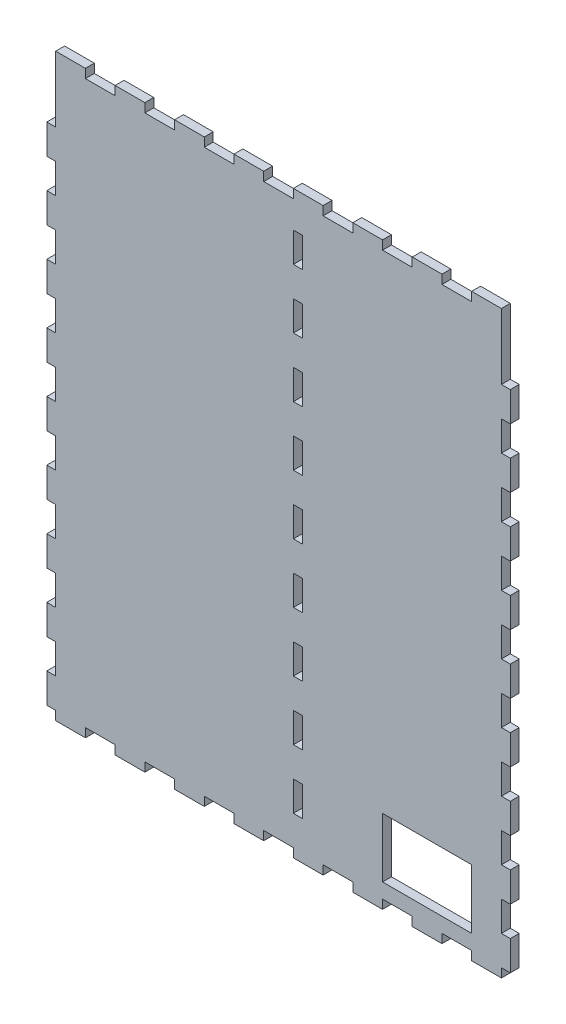
SolidWorks part; units mm, degrees
ref_plane "Plan de face" through (0, 0, 0) normal (0, 0, 1) x (1, 0, 0)
ref_plane "Plan de dessus" through (0, 0, 0) normal (0, 1, 0) x (1, 0, 0)
ref_plane "Plan de droite" through (0, 0, 0) normal (1, 0, 0) x (0, 0, -1)
sketch "Esquisse1" plane through (0, 0, 0) normal (0, 0, 1) x (1, 0, 0)
  line L1 (0, 0) -> (150, 0)
  line L2 (0, 0) -> (0, -189.15)
  line L3 (0, -189.15) -> (150, -189.15)
  line L4 (150, 0) -> (150, -189.15)
  dimension "D1" = 150
  dimension "D2" = 189.15
extrude "Boss.-Extru.1" add sketch "Esquisse1" along normal blind 3
sketch "Esquisse2" plane through (0, 0, 0) normal (0, 1, 0) x (1, 0, 0)
  line L0 (150, -3) -> (0, -3) construction
  line L1 (0, 0) -> (10, 0)
  line L2 (0, 0) -> (0, -3)
  line L3 (0, -3) -> (10, -3)
  line L4 (10, 0) -> (10, -3)
  dimension "D1" = 10
extrude "Boss.-Extru.2" add sketch "Esquisse2" along normal blind 3
pattern_linear "Répétition linéaire1" count 8 spacing 20 along (1, 0, 0) of "Boss.-Extru.2"
sketch "Esquisse3" plane through (0, -189.15, 0) normal (0, -1, 0) x (1, 0, 0)
  line L0 (0, 0) -> (150, 0) construction
  line L1 (0, 3) -> (10, 3)
  line L2 (0, 3) -> (0, 0)
  line L3 (0, 0) -> (10, 0)
  line L4 (10, 3) -> (10, 0)
  dimension "D1" = 10
extrude "Boss.-Extru.3" add sketch "Esquisse3" along normal blind 3
pattern_linear "Répétition linéaire2" count 8 spacing 20 along (1, 0, 0) of "Boss.-Extru.3"
sketch "Esquisse4" plane through (0, 0, 0) normal (-1, 0, 0) x (0, 0, 1)
  line L0 (3, 3) -> (3, -192.15) construction
  line L1 (3, -179.15) -> (0, -179.15)
  line L2 (3, -179.15) -> (3, -189.15)
  line L3 (3, -189.15) -> (0, -189.15)
  line L4 (0, -179.15) -> (0, -189.15)
  line L5 (0, 3) -> (0, -192.15) construction
  line L7 (3, -192.15) -> (0, -192.15) construction
  dimension "D1" = 10
  dimension "D2" = 3
extrude "Boss.-Extru.4" add sketch "Esquisse4" along normal blind 3
pattern_linear "Répétition linéaire3" count 9 spacing 20 along (0, 1, 0) of "Boss.-Extru.4"
sketch "Esquisse5" plane through (150, 0, 0) normal (1, 0, 0) x (0, 0, -1)
  line L0 (-3, -192.15) -> (-3, 3) construction
  line L1 (-3, -189.15) -> (0, -189.15)
  line L2 (-3, -189.15) -> (-3, -179.15)
  line L3 (-3, -179.15) -> (0, -179.15)
  line L4 (0, -189.15) -> (0, -179.15)
  line L5 (0, -192.15) -> (0, 3) construction
  line L8 (0, -192.15) -> (-3, -192.15) construction
  dimension "D1" = 10
  dimension "D2" = 3
extrude "Boss.-Extru.5" add sketch "Esquisse5" along normal blind 3
pattern_linear "Répétition linéaire4" count 9 spacing 20 along (0, 1, 0) of "Boss.-Extru.5"
sketch "Esquisse6" plane through (0, 0, 0) normal (0, 0, -1) x (-1, 0, 0)
  line L1 (-110, -184.15) -> (-140, -184.15)
  line L2 (-110, -184.15) -> (-110, -164.15)
  line L3 (-110, -164.15) -> (-140, -164.15)
  line L4 (-140, -184.15) -> (-140, -164.15)
  line L5 (-10, -189.15) -> (-20, -189.15) construction
  line L6 (-150, -179.15) -> (-150, -169.15) construction
  dimension "D1" = 30
  dimension "D2" = 20
  dimension "D3" = 10
  dimension "D4" = 5
extrude "Enlèv. mat.-Extru.1" cut sketch "Esquisse6" against normal through all
sketch "Esquisse7" plane through (0, 0, 0) normal (0, 0, -1) x (-1, 0, 0)
  line L0 (-80, 0) -> (-70, 0) construction
  line L1 (-83, -9.15) -> (-80, -9.15)
  line L2 (-83, -9.15) -> (-83, -19.15)
  line L3 (-83, -19.15) -> (-80, -19.15)
  line L4 (-80, -9.15) -> (-80, -19.15)
  line L5 (0, 3) -> (0, -19.15) construction
  dimension "D1" = 3
  dimension "D2" = 10
  dimension "D3" = 9.15
  dimension "D4" = 80
extrude "Enlèv. mat.-Extru.2" cut sketch "Esquisse7" against normal through all
pattern_linear "Répétition linéaire5" count 9 spacing 20 along (0, -1, 0) of "Enlèv. mat.-Extru.2"
